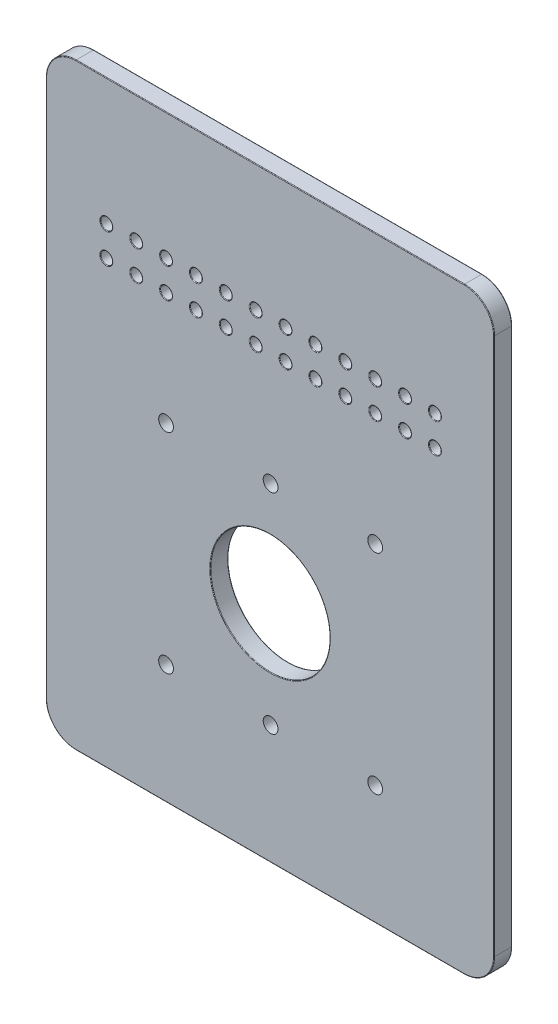
SolidWorks part; units mm, degrees
ref_plane "Front Plane" through (0, 0, 0) normal (0, 0, 1) x (1, 0, 0)
ref_plane "Top Plane" through (0, 0, 0) normal (0, 1, 0) x (1, 0, 0)
ref_plane "Right Plane" through (0, 0, 0) normal (1, 0, 0) x (0, 0, -1)
sketch "Sketch1" plane through (0, 0, 0) normal (0, 0, 1) x (1, 0, 0)
  line L0 (-54.8101, 72.6623) -> (-44.8101, 72.6623) construction
  line L1 (-65, 125) -> (65, 125)
  line L2 (-75, 115) -> (-75, -65)
  line L3 (-65, -75) -> (65, -75)
  line L4 (75, 115) -> (75, -65)
  line L5 (35.1899, 34.8551) -> (0.1899, 34.8551) construction
  line L6 (35.1899, 34.8551) -> (35.1899, -35.1449) construction
  circle A0 centre (0, 0) radius 20
  circle A1 centre (-54.8101, 72.6623) radius 2
  circle A2 centre (-44.8101, 72.6623) radius 2
  circle A3 centre (-34.8101, 72.6623) radius 2
  circle A4 centre (-24.8101, 72.6623) radius 2
  circle A5 centre (-14.8101, 72.6623) radius 2
  circle A6 centre (-4.8101, 72.6623) radius 2
  circle A7 centre (5.1899, 72.6623) radius 2
  circle A8 centre (15.1899, 72.6623) radius 2
  circle A9 centre (25.1899, 72.6623) radius 2
  circle A10 centre (35.1899, 72.6623) radius 2
  circle A11 centre (45.1899, 72.6623) radius 2
  circle A12 centre (55.1899, 72.6623) radius 2
  circle A13 centre (-44.8101, 82.6623) radius 2
  circle A14 centre (-34.8101, 82.6623) radius 2
  circle A15 centre (-24.8101, 82.6623) radius 2
  circle A16 centre (-14.8101, 82.6623) radius 2
  circle A17 centre (-4.8101, 82.6623) radius 2
  circle A18 centre (5.1899, 82.6623) radius 2
  circle A19 centre (15.1899, 82.6623) radius 2
  circle A20 centre (25.1899, 82.6623) radius 2
  circle A21 centre (35.1899, 82.6623) radius 2
  circle A22 centre (45.1899, 82.6623) radius 2
  circle A23 centre (55.1899, 82.6623) radius 2
  circle A24 centre (-54.8101, 82.6623) radius 2
  arc A25 (65, 125) -> (75, 115) centre (65, 115) cw
  arc A26 (75, -65) -> (65, -75) centre (65, -65) cw
  arc A27 (-65, -75) -> (-75, -65) centre (-65, -65) cw
  arc A28 (-75, 115) -> (-65, 125) centre (-65, 115) cw
  circle A29 centre (35.1899, 34.8551) radius 2.472
  circle A30 centre (0.1899, 34.8551) radius 2.472
  circle A31 centre (-34.8101, 34.8551) radius 2.472
  circle A32 centre (0.1899, -35.1449) radius 2.472
  circle A33 centre (-34.8101, -35.1449) radius 2.472
  circle A34 centre (35.1899, -35.1449) radius 2.472
  dimension "D5" = 12
  dimension "D8" = 10
  dimension "D9" = 10
  dimension "D1" = 150
  dimension "D2" = 200
  dimension "D3" = 75
  dimension "D4" = 75
  dimension "D7" = 10
  dimension "D12" = 35
  dimension "D13" = 70
  dimension "D6" = 2
  dimension "D10" = 3
  dimension "D11" = 2
extrude "Boss-Extrude1" add sketch "Sketch1" along normal mid plane 6
fillet "Fillet2" radius 0.2 66 edges at (0, -75, -3) (-72.0711, -72.0711, -3) (-75, 25, -3) (-52.8101, 82.6623, -3) (-52.8101, 82.6623, 3) (57.1899, 82.6623, -3) (57.1899, 82.6623, 3) (47.1899, 82.6623, -3) (47.1899, 82.6623, 3) (37.1899, 82.6623, -3) (37.1899, 82.6623, 3) (27.1899, 82.6623, -3) (27.1899, 82.6623, 3) (17.1899, 82.6623, -3) (17.1899, 82.6623, 3) (7.1899, 82.6623, -3) (7.1899, 82.6623, 3) (-2.8101, 82.6623, -3) (-2.8101, 82.6623, 3) (-12.8101, 82.6623, -3) (-12.8101, 82.6623, 3) (-22.8101, 82.6623, -3) (-22.8101, 82.6623, 3) (-32.8101, 82.6623, -3) (-32.8101, 82.6623, 3) (-42.8101, 82.6623, -3) (-42.8101, 82.6623, 3) (57.1899, 72.6623, -3) (57.1899, 72.6623, 3) (47.1899, 72.6623, -3) (47.1899, 72.6623, 3) (37.1899, 72.6623, -3) (37.1899, 72.6623, 3) (27.1899, 72.6623, -3) (27.1899, 72.6623, 3) (17.1899, 72.6623, -3) (17.1899, 72.6623, 3) (7.1899, 72.6623, -3) (7.1899, 72.6623, 3) (-2.8101, 72.6623, -3) (-2.8101, 72.6623, 3) (-12.8101, 72.6623, -3) (-12.8101, 72.6623, 3) (-22.8101, 72.6623, -3) (-22.8101, 72.6623, 3) (-32.8101, 72.6623, -3) (-32.8101, 72.6623, 3) (-42.8101, 72.6623, -3) (-42.8101, 72.6623, 3) (-52.8101, 72.6623, -3) (-52.8101, 72.6623, 3) (20, 0, -3) (20, 0, 3) (72.0711, 122.0711, -3) (0, 125, -3) (-72.0711, 122.0711, -3) (72.0711, -72.0711, -3) (75, 25, -3) (72.0711, 122.0711, 3) (0, 125, 3) (-72.0711, 122.0711, 3) (-75, 25, 3) (-72.0711, -72.0711, 3) (0, -75, 3) (72.0711, -72.0711, 3) (75, 25, 3)
